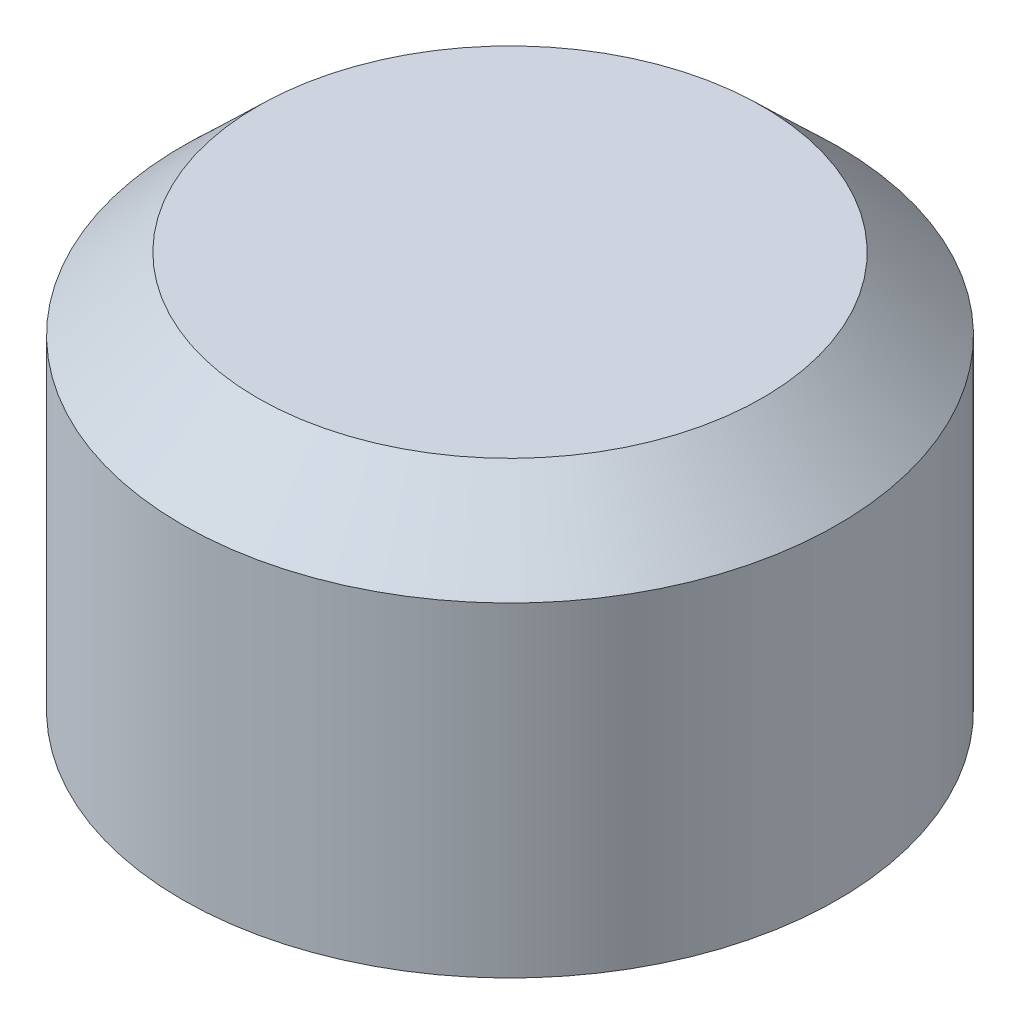
SolidWorks part; units mm, degrees
ref_plane "Front Plane" through (0, 0, 0) normal (0, 0, 1) x (1, 0, 0)
ref_plane "Top Plane" through (0, 0, 0) normal (0, 1, 0) x (1, 0, 0)
ref_plane "Right Plane" through (0, 0, 0) normal (1, 0, 0) x (0, 0, -1)
sketch "Sketch1" plane through (0, 0, 0) normal (0, 0, 1) x (1, 0, 0)
  line L0 (-2438.4, 0) -> (-2438.4, 2753.721)
  line L1 (-2438.4, 2753.721) -> (-2118.721, 3073.4)
  line L2 (-2118.721, 3073.4) -> (-1190.8772, 3073.4)
  line L3 (-1190.8772, 3073.4) -> (-914.4, 2796.9228)
  line L4 (-914.4, 2796.9228) -> (-914.4, 2074)
  line L6 (-939.8, 2074) -> (-939.8, 2786.4018)
  line L7 (-939.8, 2786.4018) -> (-1201.3982, 3048)
  line L8 (-1201.3982, 3048) -> (-2108.2, 3048)
  line L9 (-2108.2, 3048) -> (-2413, 2743.2)
  line L10 (-2413, 2743.2) -> (-2413, 0)
  line L11 (-2413, 0) -> (-2438.4, 0)
  line L12 (-914.4, 2074) -> (-597.0312, 1524.3011)
  line L13 (-597.0312, 1524.3011) -> (-622.4312, 1524.3011)
  line L14 (-622.4312, 1524.3011) -> (-939.8, 2074)
  point P2 (-939.8, 2074)
  point P14 (-914.4, 2074)
  dimension "D1" = 25.4
  dimension "D3" = 2743.2
  dimension "D4" = 304.8
  dimension "D5" = 304.8
  dimension "D6" = 25.4
  dimension "D8" = 25.4
  dimension "D9" = 25.4
  dimension "D11" = 2438.4
  dimension "D13" = 30
  dimension "D14" = 25.4
sketch "Sketch2" plane through (0, 0, 0) normal (0, 0, 1) x (1, 0, 0)
  line L0 (-2743.2, 0) -> (-2768.6, 0)
  line L1 (-2768.6, 0) -> (-2768.6, 2743.2)
  line L2 (-2743.2, 0) -> (-2743.2, 2732.3741)
  line L3 (-2743.2, 2732.3741) -> (-2123.3813, 3327.4)
  line L4 (-2123.3813, 3327.4) -> (0, 3327.4)
  line L5 (0, 3327.4) -> (0, 3352.8)
  line L6 (0, 3352.8) -> (-2133.6, 3352.8)
  line L7 (-2133.6, 3352.8) -> (-2768.6, 2743.2)
  dimension "D1" = 2743.2
  dimension "D2" = 2133.6
  dimension "D3" = 25.4
  dimension "D4" = 25.4
  dimension "D5" = 304.8
  dimension "D6" = 609.6
  dimension "D7" = 25.4
ref_axis "Axis1" through (0, 3520.44, 0) along (0, -1, 0)
revolve "Revolve1" add sketch "Sketch1" angle 360 about axis through (0, 3520.44, 0) along (0, -1, 0)
revolve "Revolve2" add sketch "Sketch2" angle 360 about axis through (0, 3520.44, 0) along (0, -1, 0)
